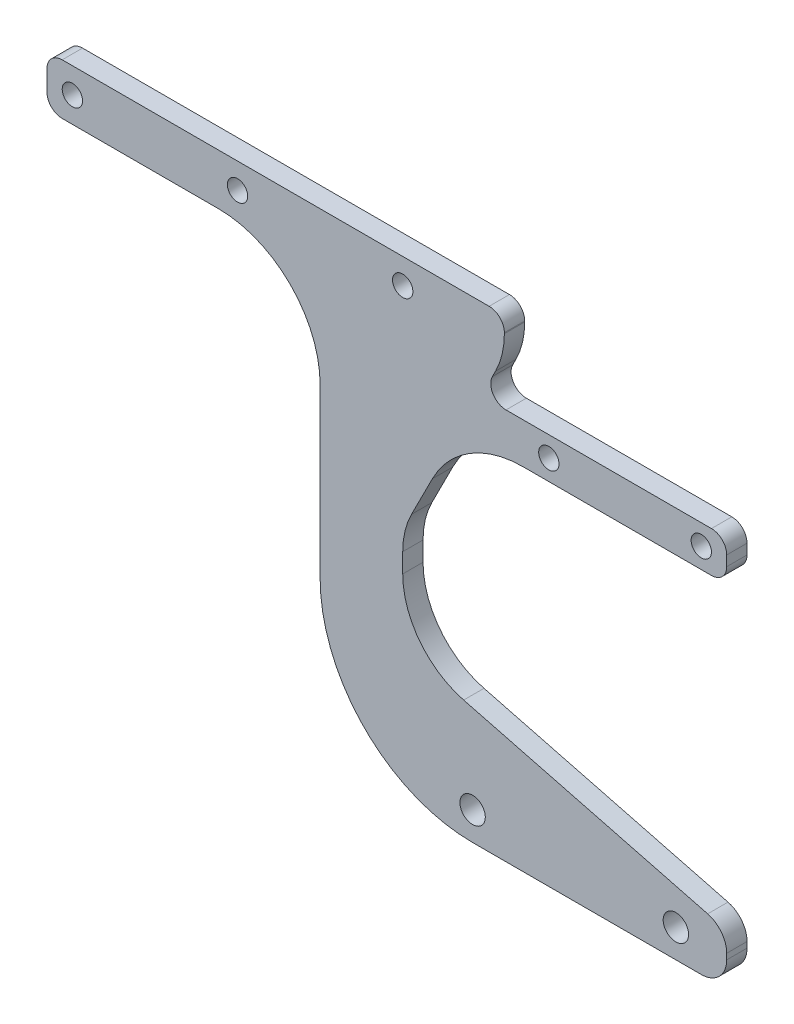
SolidWorks part; units mm, degrees
ref_plane "Front Plane" through (0, 0, 0) normal (0, 0, 1) x (1, 0, 0)
ref_plane "Top Plane" through (0, 0, 0) normal (0, 1, 0) x (1, 0, 0)
ref_plane "Right Plane" through (0, 0, 0) normal (1, 0, 0) x (0, 0, -1)
sketch "Sketch1" plane through (0, 0, 0) normal (0, 0, 1) x (1, 0, 0)
  line L0 (3, 0) -> (33.75, 0)
  line L1 (0, 3) -> (0, 7)
  line L2 (3, 10) -> (87, 10)
  line L3 (90, 7) -> (90, 6.8198)
  line L4 (0, 5) -> (90, 5) construction
  line L5 (0, 5) -> (5, 5)
  line L6 (37.5, 5) -> (70, 5)
  line L7 (53.75, -53) -> (53.75, -20)
  line L8 (53.75, 5) -> (53.75, -14) construction
  line L10 (70, -40.3198) -> (70, -44.1139)
  line L11 (83.75, -83) -> (128.75, -83)
  line L12 (133.75, -78) -> (133.75, -76.8706)
  line L13 (88.2745, -0.4078) -> (87.6475, -1.6463)
  line L14 (81.9909, -59.6035) -> (130.0028, -72.0301)
  line L15 (93.6834, -14) -> (130.751, -14)
  line L16 (133.75, -11.001) -> (133.75, -8.999)
  line L17 (130.751, -6) -> (90.323, -6)
  line L18 (93.6834, -14) -> (95.9045, -14) construction
  line L19 (75.8403, -24.9655) -> (71.7255, -33.0922)
  arc A1 (3, 0) -> (0, 3) centre (3, 3) cw
  arc A2 (3, 10) -> (0, 7) centre (3, 7) ccw
  arc A3 (87, 10) -> (90, 7) centre (87, 7) cw
  circle A4 centre (5, 5) radius 2
  circle A5 centre (37.5, 5) radius 2
  circle A6 centre (70, 5) radius 2
  arc A7 (53.75, -53) -> (83.75, -83) centre (83.75, -53) ccw
  arc A8 (53.75, -20) -> (33.75, 0) centre (33.75, -20) ccw
  arc A9 (128.75, -83) -> (133.75, -78) centre (128.75, -78) ccw
  arc A10 (133.75, -76.8706) -> (130.0028, -72.0301) centre (128.75, -76.8706) ccw
  arc A11 (71.7255, -33.0922) -> (70, -40.3198) centre (86, -40.3198) ccw
  arc A12 (70, -44.1139) -> (81.9909, -59.6035) centre (86, -44.1139) ccw
  circle A13 centre (83.75, -77.4353) radius 2.5
  circle A14 centre (123.75, -77.4353) radius 2.5
  arc A15 (90, 6.8198) -> (88.2745, -0.4078) centre (74, 6.8198) cw
  arc A16 (90.323, -6) -> (87.6475, -1.6463) centre (90.323, -3.001) cw
  arc A17 (133.75, -8.999) -> (130.751, -6) centre (130.751, -8.999) ccw
  arc A18 (130.751, -14) -> (133.75, -11.001) centre (130.751, -11.001) ccw
  arc A19 (75.8403, -24.9655) -> (93.6834, -14) centre (93.6834, -34) cw
  circle A20 centre (128.75, -10) radius 2.001
  circle A21 centre (98.75, -10) radius 2.001
  point P9 (0, 0)
  point P63 (98.75, -10)
  dimension "D1" = 5
  dimension "D2" = 3
  dimension "D3" = 30
  dimension "D4" = 20
  dimension "D5" = 16
  dimension "D6" = 16
  dimension "D7" = 2.999
  dimension "D8" = 20
  dimension "D9" = 2
extrude "Boss-Extrude1" add sketch "Sketch1" along normal blind 4
